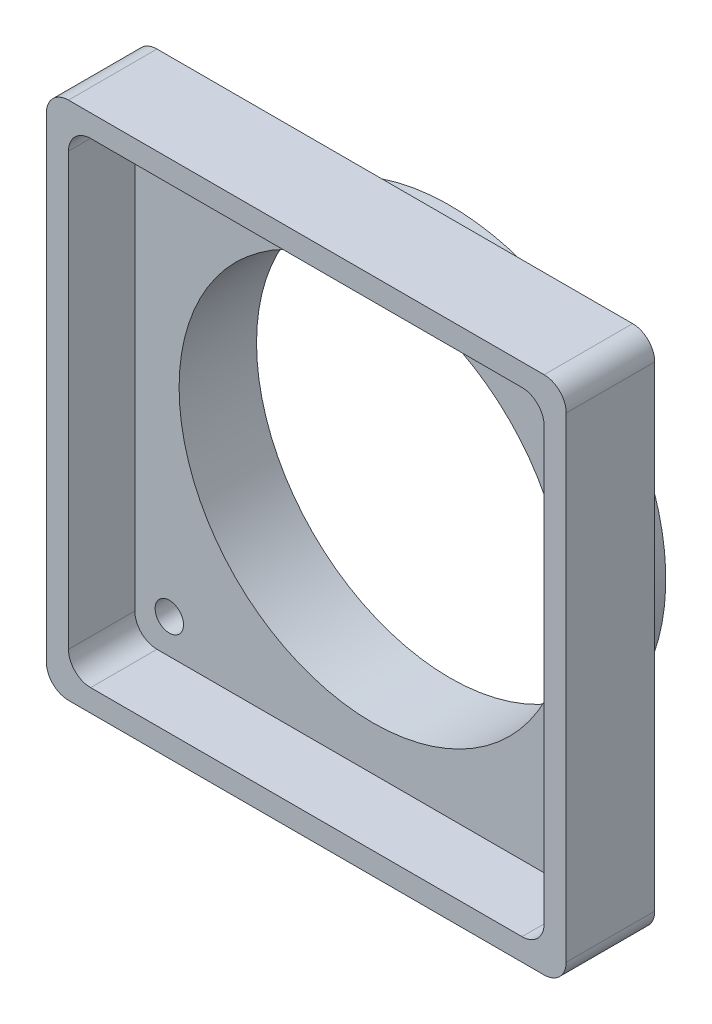
SolidWorks part; units mm, degrees
ref_plane "Front Plane" through (0, 0, 0) normal (0, 0, 1) x (1, 0, 0)
ref_plane "Top Plane" through (0, 0, 0) normal (0, 1, 0) x (1, 0, 0)
ref_plane "Right Plane" through (0, 0, 0) normal (1, 0, 0) x (0, 0, -1)
sketch "Sketch1" plane through (0, 0, 0) normal (0, 0, 1) x (1, 0, 0)
  line L1 (-27.305, 29.845) -> (27.305, 29.845)
  line L2 (-29.845, 27.305) -> (-29.845, -27.305)
  line L3 (-27.305, -29.845) -> (27.305, -29.845)
  line L4 (29.845, 27.305) -> (29.845, -27.305)
  arc A0 (-29.845, -27.305) -> (-27.305, -29.845) centre (-27.305, -27.305) ccw
  arc A1 (27.305, -29.845) -> (29.845, -27.305) centre (27.305, -27.305) ccw
  arc A2 (27.305, 29.845) -> (29.845, 27.305) centre (27.305, 27.305) cw
  arc A3 (-27.305, 29.845) -> (-29.845, 27.305) centre (-27.305, 27.305) ccw
  point P7 (-29.845, -29.845)
  point P12 (29.845, 29.845)
  point P15 (-29.845, 29.845)
  dimension "D5" = 2.54
  dimension "D1" = 59.69
  dimension "D2" = 59.69
  dimension "D3" = 29.845
  dimension "D4" = 29.845
extrude "Boss-Extrude1" add sketch "Sketch1" along normal blind 16.51
sketch "Sketch2" plane through (0, 0, 16.51) normal (0, 0, 1) x (1, 0, 0)
  circle A0 centre (0, 0) radius 22.225
  dimension "D1" = 44.45
extrude "Cut-Extrude1" cut sketch "Sketch2" against normal through all
sketch "Sketch4" plane through (0, 0, 0) normal (0, 0, -1) x (-1, 0, 0)
  circle A0 centre (0, 0) radius 24.765
  dimension "D1" = 49.53
extrude "Cut-Extrude2" cut sketch "Sketch4" against normal blind 6.35 flip side to cut
sketch "Sketch3" plane through (0, 0, 16.51) normal (0, 0, 1) x (1, 0, 0)
  line L0 (27.305, 29.845) -> (-27.305, 29.845) construction
  line L1 (24.765, -27.305) -> (-24.765, -27.305)
  line L2 (27.305, -24.765) -> (27.305, 24.765)
  line L3 (24.765, 27.305) -> (-24.765, 27.305)
  line L4 (-27.305, -24.765) -> (-27.305, 24.765)
  line L6 (-27.305, -29.845) -> (27.305, -29.845) construction
  line L7 (-29.845, 27.305) -> (-29.845, -27.305) construction
  line L8 (29.845, -27.305) -> (29.845, 27.305) construction
  arc A0 (-24.765, -27.305) -> (-27.305, -24.765) centre (-24.765, -24.765) cw
  arc A1 (24.765, -27.305) -> (27.305, -24.765) centre (24.765, -24.765) ccw
  arc A2 (27.305, 24.765) -> (24.765, 27.305) centre (24.765, 24.765) ccw
  arc A3 (-24.765, 27.305) -> (-27.305, 24.765) centre (-24.765, 24.765) ccw
  dimension "D5" = 2.54
  dimension "D1" = 2.54
  dimension "D2" = 2.54
  dimension "D3" = 2.54
  dimension "D4" = 2.54
extrude "Cut-Extrude3" cut sketch "Sketch3" against normal offset from surface (7.62 mm away) 2.54 up to face at (-24.765, 0, 6.35)
hole_wizard "#4 Clearance Hole1" positions "Sketch5" profile "Sketch6" hole size "#4" standard "ANSI Inch"
sketch "Sketch5" plane through (0, 0, 8.89) normal (0, 0, 1) x (1, 0, 0)
  line L0 (0, 0) -> (-22.4722, 22.4722) construction
  line L3 (0, 0) -> (-38.6249, 0) construction
  point P0 (-23.3487, 23.3487)
  dimension "D1" = 33.02
  dimension "D2" = 45
sketch "Sketch6" plane through (-23.3487, 23.3487, 8.89) normal (1, 0, 0) x (0, -1, 0)
  line L0 (0, 0) -> (0, 8.5752)
  line L1 (0, 8.5752) -> (1.6319, 7.5946)
  line L2 (1.6319, 7.5946) -> (1.6319, 0)
  line L5 (1.6319, 0) -> (0, 0)
  line L10 (0, 8.5752) -> (-1.632, 7.5946) construction
  line L11 (0, -6.35) -> (0, 107.95) construction
  dimension "Hole Dia." = 3.2639
  dimension "Hole Depth" = 7.5946
  dimension "Drill Angle" = 118
pattern_circular "CirPattern1" count 4 over 360 about axis through (0, 0, 0) along (0, 0, 1) of "#4 Clearance Hole1"
equation "\"D2@Sketch1\"=\"D1@Sketch1\""
equation "\"D3@Sketch1\"=\"D1@Sketch1\"/2"
equation "\"D4@Sketch1\"=\"D2@Sketch1\"/2"
equation "\"D2@Sketch3\"=\"D1@Sketch3\""
equation "\"D3@Sketch3\"=\"D1@Sketch3\""
equation "\"D4@Sketch3\"=\"D3@Sketch3\""
